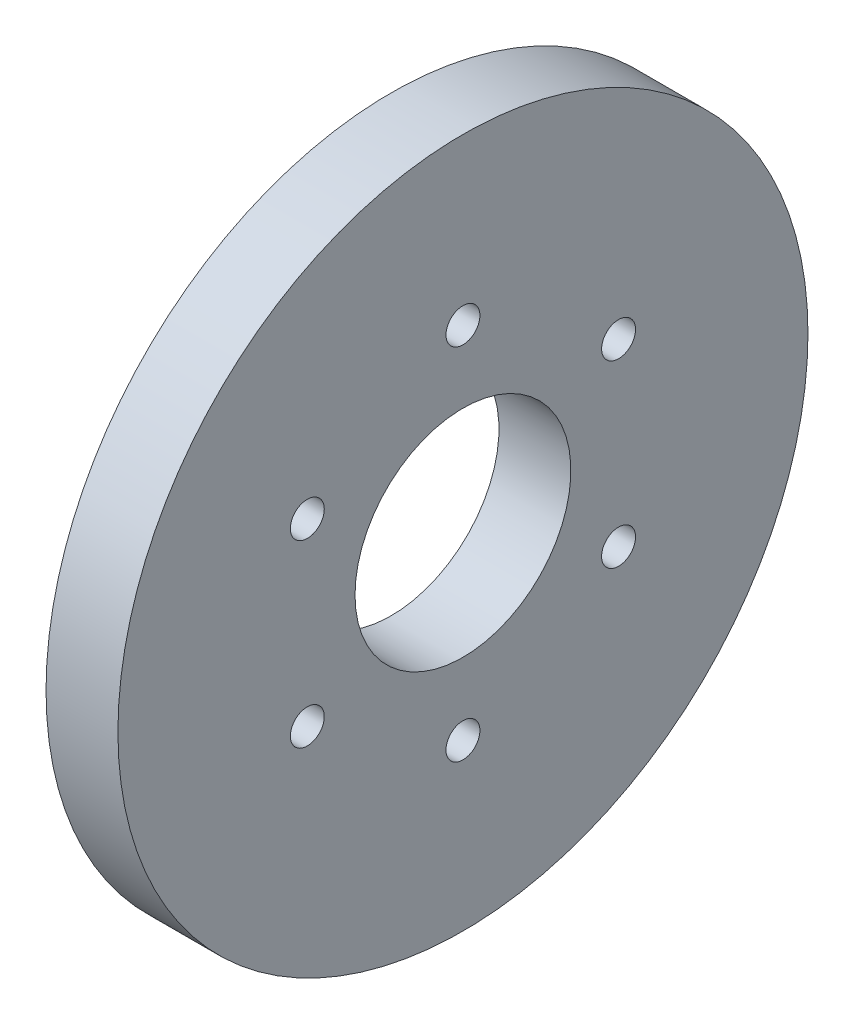
SolidWorks part; units mm, degrees
ref_plane "Front Plane" through (0, 0, 0) normal (0, 0, 1) x (1, 0, 0)
ref_plane "Top Plane" through (0, 0, 0) normal (0, 1, 0) x (1, 0, 0)
ref_plane "Right Plane" through (0, 0, 0) normal (1, 0, 0) x (0, 0, -1)
sketch "Sketch1" plane through (0, 0, 0) normal (1, 0, 0) x (0, 0, -1)
  circle A0 centre (0, 0) radius 45.72
  dimension "D1" = 91.44
extrude "Boss-Extrude1" add sketch "Sketch1" along normal blind 9.525
sketch "Sketch2" plane through (0, 0, 0) normal (-1, 0, 0) x (0, 0, 1)
  circle A0 centre (0, 0) radius 14.3002
  dimension "D1" = 28.6004
extrude "Cut-Extrude1" cut sketch "Sketch2" against normal through all
hole_wizard "#8 Clearance Hole1" positions "Sketch3" profile "Sketch4" hole size "#8" standard "ANSI Inch" end condition through all
sketch "Sketch3" plane through (0, 0, 0) normal (-1, 0, 0) x (0, 0, 1)
  point P0 (0, 23.8125)
  dimension "D1" = 23.8125
sketch "Sketch4" plane through (0, 23.8125, 0) normal (0, 1, 0) x (0, 0, 1)
  line L0 (0, 0) -> (0, 9.525)
  line L1 (0, 9.525) -> (2.2479, 9.525)
  line L2 (2.2479, 9.525) -> (2.2479, 0)
  line L5 (2.2479, 0) -> (0, 0)
  line L11 (0, -6.35) -> (0, 107.95) construction
  dimension "Thru Hole Dia." = 4.4958
  dimension "Thru Hole Depth" = 9.525
pattern_circular "CirPattern1" count 6 over 360 about axis through (0, 0, 0) along (1, 0, 0) of "#8 Clearance Hole1"
